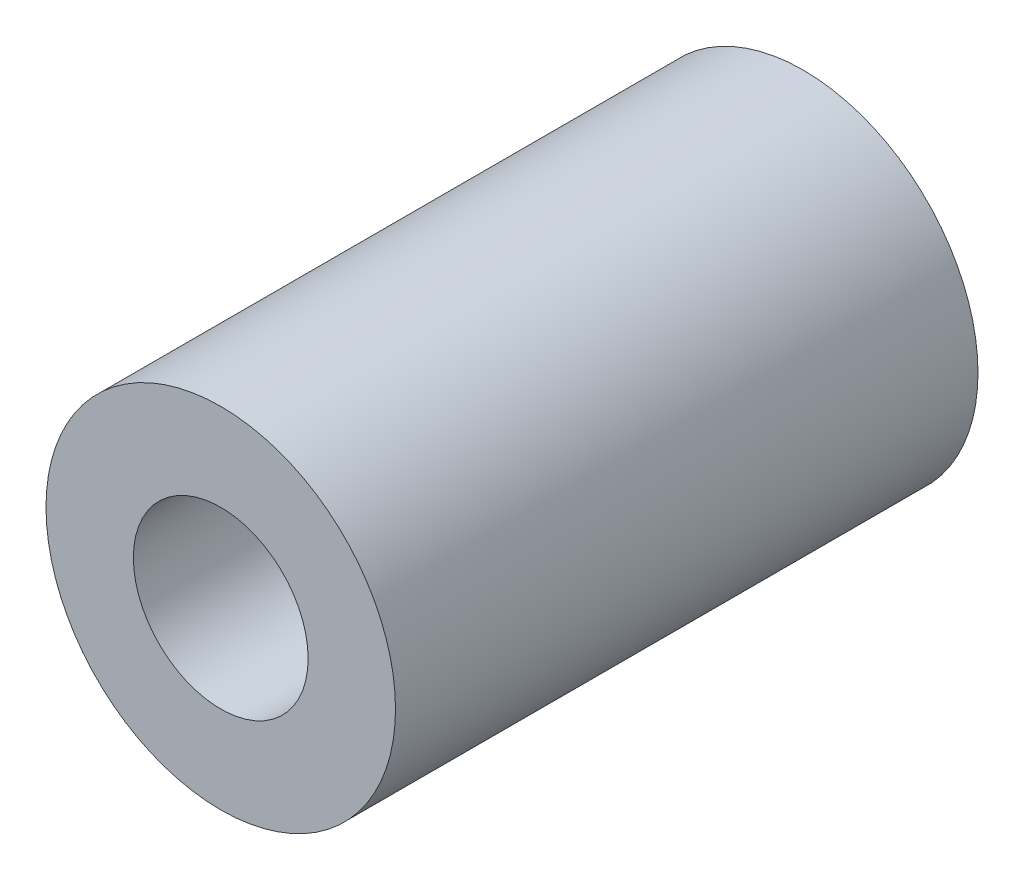
SolidWorks part; units mm, degrees
ref_plane "前视基准面" through (0, 0, 0) normal (0, 0, 1) x (1, 0, 0)
ref_plane "上视基准面" through (0, 0, 0) normal (0, 1, 0) x (1, 0, 0)
ref_plane "右视基准面" through (0, 0, 0) normal (1, 0, 0) x (0, 0, -1)
sketch "草图1" plane through (0, 0, 0) normal (0, 0, 1) x (1, 0, 0)
  circle A0 centre (0, 0) radius 3
  circle A1 centre (0, 0) radius 1.5
  dimension "D1" = 3
  dimension "D2" = 6
extrude "凸台-拉伸1" add sketch "草图1" along normal mid plane 10
